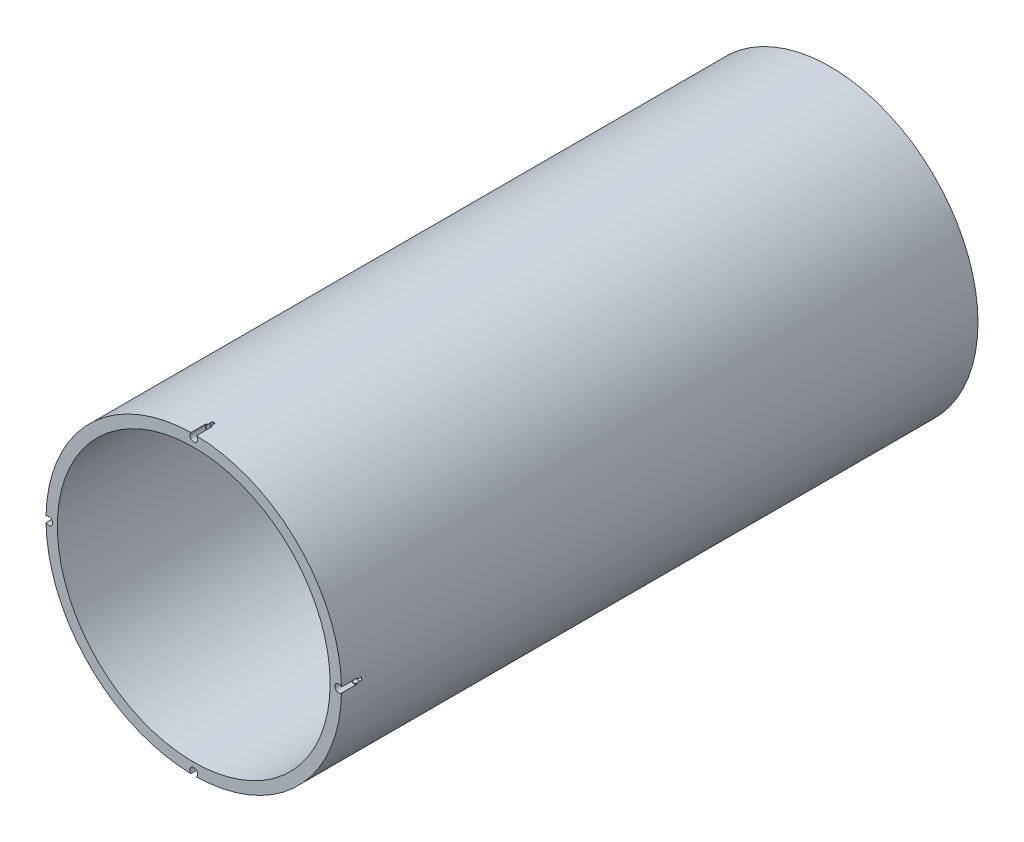
SolidWorks part; units mm, degrees
material "6061 Alloy"
ref_plane "Front Plane" through (0, 0, 0) normal (0, 0, 1) x (1, 0, 0)
ref_plane "Top Plane" through (0, 0, 0) normal (0, 1, 0) x (1, 0, 0)
ref_plane "Right Plane" through (0, 0, 0) normal (1, 0, 0) x (0, 0, -1)
sketch "Sketch1" plane through (0, 0, 0) normal (0, 0, 1) x (1, 0, 0)
  line L1 (27.94, 21.463) -> (-27.94, 21.463) construction
  line L2 (27.94, 21.463) -> (27.94, -21.463) construction
  line L3 (27.94, -21.463) -> (-27.94, -21.463) construction
  line L4 (-27.94, 21.463) -> (-27.94, -21.463) construction
  line L5 (27.94, 21.463) -> (-27.94, -21.463) construction
  line L6 (27.94, -21.463) -> (-27.94, 21.463) construction
  circle A0 centre (0, 0) radius 38.1
  circle A1 centre (0, 0) radius 41.275
  point P0 (0, 0)
  dimension "D3" = 76.2
  dimension "D1" = 42.926
  dimension "D2" = 55.88
  dimension "D4" = 3.175
extrude "Boss-Extrude1" add sketch "Sketch1" along normal blind 177.8
hole_wizard "#2-56 Tapped Hole1" positions "Sketch3" profile "Sketch2" tap size "#2-56" standard "Ansi Inch"
sketch "Sketch3" plane through (0, 0, 177.8) normal (0, 0, 1) x (1, 0, 0)
  line L0 (-41.275, 0) -> (41.275, 0) construction
  line L2 (0, 41.275) -> (0, -41.275) construction
  circle A0 centre (0, 0) radius 41.275 construction
  circle A1 centre (0, 0) radius 40.4813
  point P0 (0, 40.4812)
  point P17 (40.4812, 0)
  point P19 (0, -40.4812)
  point P21 (-40.4812, 0)
  dimension "D1" = 80.9625
sketch "Sketch2" plane through (0, 40.4812, 177.8) normal (1, 0, 0) x (0, -1, 0)
  line L0 (0, 0) -> (0, 6.1222)
  line L1 (0, 6.1222) -> (0.889, 5.588)
  line L2 (0.889, 5.588) -> (0.889, 4.318)
  line L3 (0.889, 4.318) -> (1.0922, 4.318)
  line L4 (1.0922, 4.318) -> (1.0922, 0)
  line L5 (1.0922, 0) -> (0, 0)
  line L10 (0, 6.1222) -> (-0.889, 5.588) construction
  line L11 (0, -6.35) -> (0, 107.95) construction
  dimension "Tap Drill Dia." = 1.778
  dimension "Tap Drill Depth" = 5.588
  dimension "Thread Major Dia." = 2.1844
  dimension "Thread Depth" = 4.318
  dimension "Drill Angle" = 118
